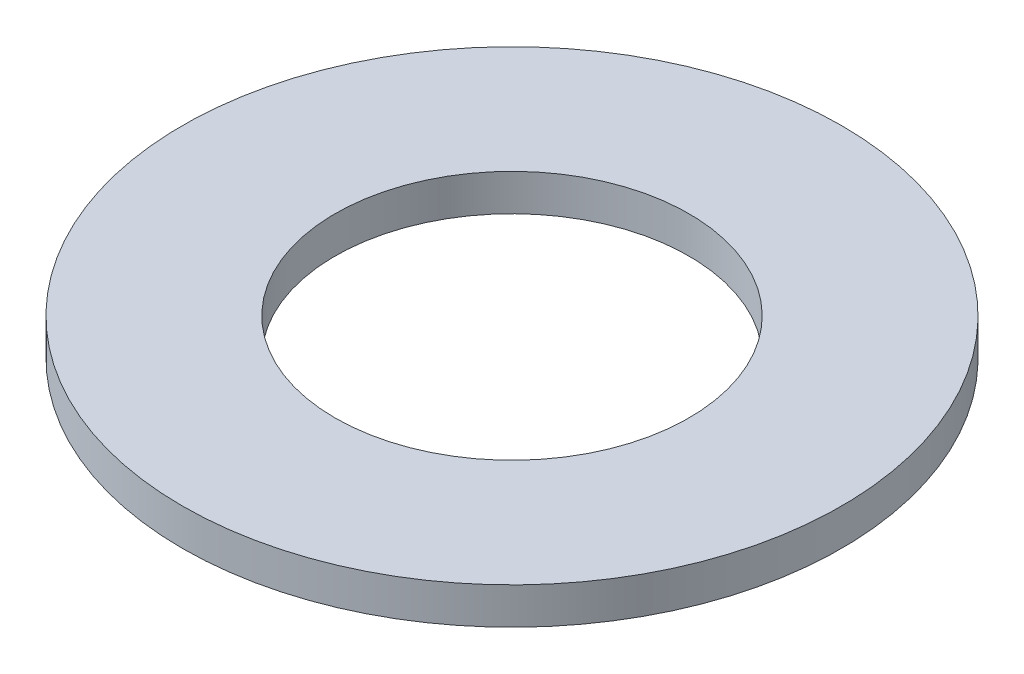
SolidWorks part; units mm, degrees
ref_plane "Front Plane" through (0, 0, 0) normal (0, 0, 1) x (1, 0, 0)
ref_plane "Top Plane" through (0, 0, 0) normal (0, 1, 0) x (1, 0, 0)
ref_plane "Right Plane" through (0, 0, 0) normal (1, 0, 0) x (0, 0, -1)
sketch "Sketch1" plane through (0, 0, 0) normal (0, 1, 0) x (1, 0, 0)
  circle A0 centre (0, 0) radius 9.4615
  circle A1 centre (0, 0) radius 5.08
extrude "Boss-Extrude1" add sketch "Sketch1" along normal blind 1.0541
